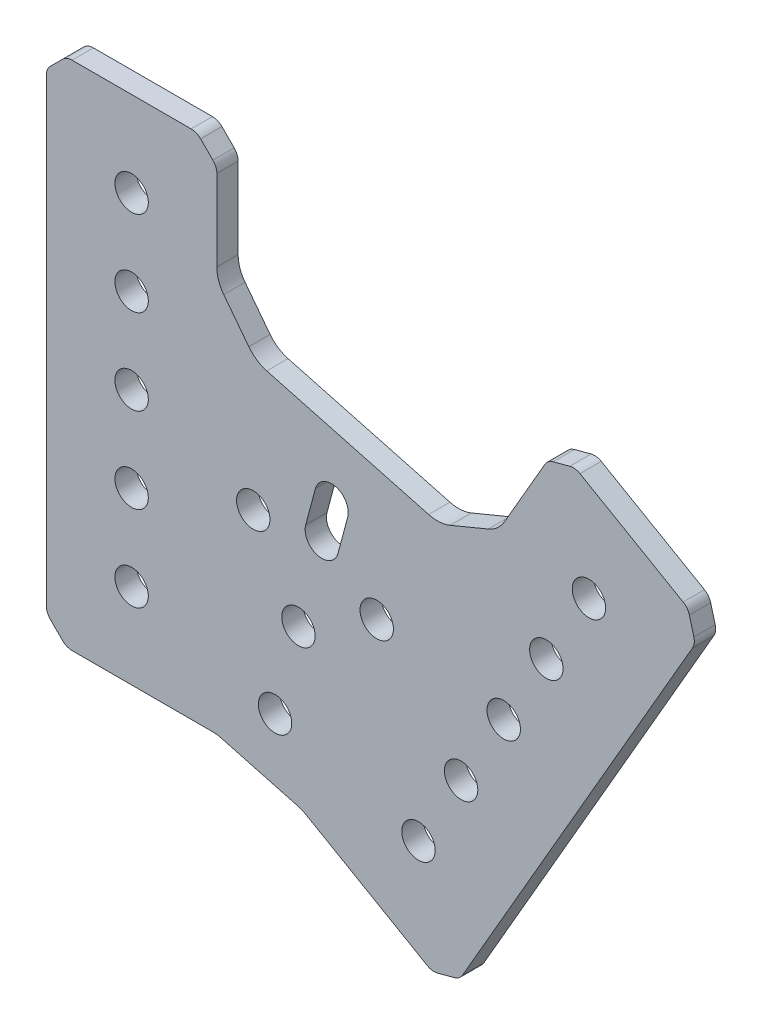
SolidWorks part; units mm, degrees
material "5052-H32"
ref_plane "Front Plane" through (0, 0, 0) normal (0, 0, 1) x (1, 0, 0)
ref_plane "Top Plane" through (0, 0, 0) normal (0, 1, 0) x (1, 0, 0)
ref_plane "Right Plane" through (0, 0, 0) normal (1, 0, 0) x (0, 0, -1)
ref_plane "Plane1" through (0, 0, 0) normal (0, 0, -1) x (-1, 0, 0)
sketch "Sketch1" plane through (0, 0, 0) normal (0, 0, -1) x (-1, 0, 0)
  line L0 (-43.4514, 32.3513) -> (-44.8955, 37.7408)
  line L1 (-40.0868, 39.0293) -> (-38.6427, 33.6398)
  line L2 (-2.4142, 0.5858) -> (-0.5858, 2.4142)
  line L3 (0, 3.8284) -> (0, 72.3716)
  line L4 (-0.5858, 73.7858) -> (-2.4142, 75.6142)
  line L5 (-3.8284, 76.2) -> (-21.5716, 76.2)
  line L6 (-22.9858, 75.6142) -> (-24.8142, 73.7858)
  line L7 (-25.4, 72.3716) -> (-25.4, 60.2893)
  line L8 (-26.4332, 57.2455) -> (-30.1623, 52.3857)
  line L9 (-32.835, 50.5998) -> (-56.961, 44.1353)
  line L10 (-60.1685, 44.3455) -> (-65.8279, 46.6897)
  line L11 (-68.2447, 48.8091) -> (-74.2858, 59.2727)
  line L12 (-75.5002, 60.2045) -> (-77.9979, 60.8738)
  line L13 (-79.5155, 60.674) -> (-94.8815, 51.8024)
  line L14 (-95.8134, 50.588) -> (-96.4826, 48.0903)
  line L15 (-96.2828, 46.5727) -> (-62.0113, -12.7874)
  line L16 (-60.7968, -13.7193) -> (-58.2992, -14.3885)
  line L17 (-56.7815, -14.1887) -> (-38.6701, -3.7321)
  line L18 (-37.4642, -3.2326) -> (-26.0358, -0.1704)
  line L19 (-24.7417, 0) -> (-3.8284, 0)
  line L20 (-55.4485, 1.2456) -> (-80.8485, 45.2397) construction
  line L21 (-34.0743, 6.9728) -> (-42.4912, 38.3851) construction
  circle A0 centre (-12.7, 12.7) radius 2.4892
  circle A1 centre (-61.7985, 12.2441) radius 2.4892
  circle A2 centre (-74.4985, 34.2411) radius 2.4892
  circle A3 centre (-12.7, 25.4) radius 2.4892
  circle A4 centre (-80.8485, 45.2397) radius 2.4892
  circle A5 centre (-68.1485, 23.2426) radius 2.4892
  circle A6 centre (-55.4485, 1.2456) radius 2.4892
  circle A7 centre (-12.7, 38.1) radius 2.4892
  circle A8 centre (-30.8255, 31.6499) radius 2.4892
  circle A9 centre (-12.7, 50.8) radius 2.4892
  circle A10 centre (-12.7, 63.5) radius 2.4892
  circle A11 centre (-49.2263, 26.7194) radius 2.4892
  circle A12 centre (-37.5607, 19.9842) radius 2.4892
  circle A13 centre (-34.0743, 6.9728) radius 2.4892
  arc A14 (-44.8955, 37.7408) -> (-40.0868, 39.0293) centre (-42.4912, 38.3851) cw
  arc A15 (-38.6427, 33.6398) -> (-43.4514, 32.3513) centre (-41.047, 32.9956) cw
  arc A16 (-0.5858, 2.4142) -> (0, 3.8284) centre (-2, 3.8284) ccw
  arc A17 (0, 72.3716) -> (-0.5858, 73.7858) centre (-2, 72.3716) ccw
  arc A18 (-2.4142, 75.6142) -> (-3.8284, 76.2) centre (-3.8284, 74.2) ccw
  arc A19 (-21.5716, 76.2) -> (-22.9858, 75.6142) centre (-21.5716, 74.2) ccw
  arc A20 (-24.8142, 73.7858) -> (-25.4, 72.3716) centre (-23.4, 72.3716) ccw
  arc A21 (-25.4, 60.2893) -> (-26.4332, 57.2455) centre (-30.4, 60.2893) cw
  arc A22 (-30.1623, 52.3857) -> (-32.835, 50.5998) centre (-34.1291, 55.4295) cw
  arc A23 (-56.961, 44.1353) -> (-60.1685, 44.3455) centre (-58.2551, 48.9649) cw
  arc A24 (-65.8279, 46.6897) -> (-68.2447, 48.8091) centre (-63.9145, 51.3091) cw
  arc A25 (-74.2858, 59.2727) -> (-75.5002, 60.2045) centre (-76.0178, 58.2727) ccw
  arc A26 (-77.9979, 60.8738) -> (-79.5155, 60.674) centre (-78.5155, 58.9419) ccw
  arc A27 (-94.8815, 51.8024) -> (-95.8134, 50.588) centre (-93.8815, 50.0703) ccw
  arc A28 (-96.4826, 48.0903) -> (-96.2828, 46.5727) centre (-94.5508, 47.5727) ccw
  arc A29 (-62.0113, -12.7874) -> (-60.7968, -13.7193) centre (-60.2792, -11.7874) ccw
  arc A30 (-58.2992, -14.3885) -> (-56.7815, -14.1887) centre (-57.7815, -12.4567) ccw
  arc A31 (-38.6701, -3.7321) -> (-37.4642, -3.2326) centre (-36.1701, -8.0622) cw
  arc A32 (-26.0358, -0.1704) -> (-24.7417, 0) centre (-24.7417, -5) cw
  arc A33 (-3.8284, 0) -> (-2.4142, 0.5858) centre (-3.8284, 2) ccw
  dimension "D2" = 4.9784
  dimension "D5" = 4.9784
  dimension "D6" = 0.5858
  dimension "D7" = 4.9784
  dimension "D8" = 2
  dimension "D9" = 2
  dimension "D10" = 2
  dimension "D11" = 2
  dimension "D12" = 2
  dimension "D13" = 5
  dimension "D14" = 5
  dimension "D15" = 5
  dimension "D16" = 5
  dimension "D17" = 2
  dimension "D18" = 2
  dimension "D19" = 2
  dimension "D20" = 2
  dimension "D21" = 2
  dimension "D22" = 2
  dimension "D23" = 5
  dimension "D24" = 5
  dimension "D25" = 2
  dimension "D1" = 76.2
  dimension "D3" = 12.7
  dimension "D4" = 12.7
  dimension "D26" = 0.5858
  dimension "D27" = 2
  dimension "D28" = 2.4142
  dimension "D29" = 2.4142
  dimension "D30" = 21.5716
  dimension "D31" = 22.9858
  dimension "D32" = 23.4
  dimension "D33" = 12.7
  dimension "D34" = 12.7
  dimension "D35" = 24.7417
  dimension "D36" = 26.0358
  dimension "D37" = 26.4332
  dimension "D38" = 30.1623
  dimension "D39" = 30.8255
  dimension "D40" = 32.835
  dimension "D41" = 34.0743
  dimension "D42" = 36.1701
  dimension "D43" = 37.5607
  dimension "D44" = 38.6427
  dimension "D45" = 38.6701
  dimension "D46" = 40.0868
  dimension "D47" = 41.047
  dimension "D48" = 49.2263
  dimension "D49" = 55.4485
  dimension "D50" = 56.7815
  dimension "D51" = 56.961
  dimension "D52" = 58.2992
  dimension "D53" = 60.1685
  dimension "D54" = 60.2792
  dimension "D55" = 61.7985
  dimension "D56" = 63.9145
  dimension "D57" = 68.1485
  dimension "D58" = 68.2447
  dimension "D59" = 74.2858
  dimension "D60" = 74.4985
  dimension "D61" = 75.5002
  dimension "D62" = 77.9979
  dimension "D63" = 79.5155
  dimension "D64" = 93.8815
  dimension "D65" = 94.5508
  dimension "D66" = 95.8134
  dimension "D67" = 0.5858
extrude "Boss-Extrude1" add sketch "Sketch1" against normal blind 3.175
